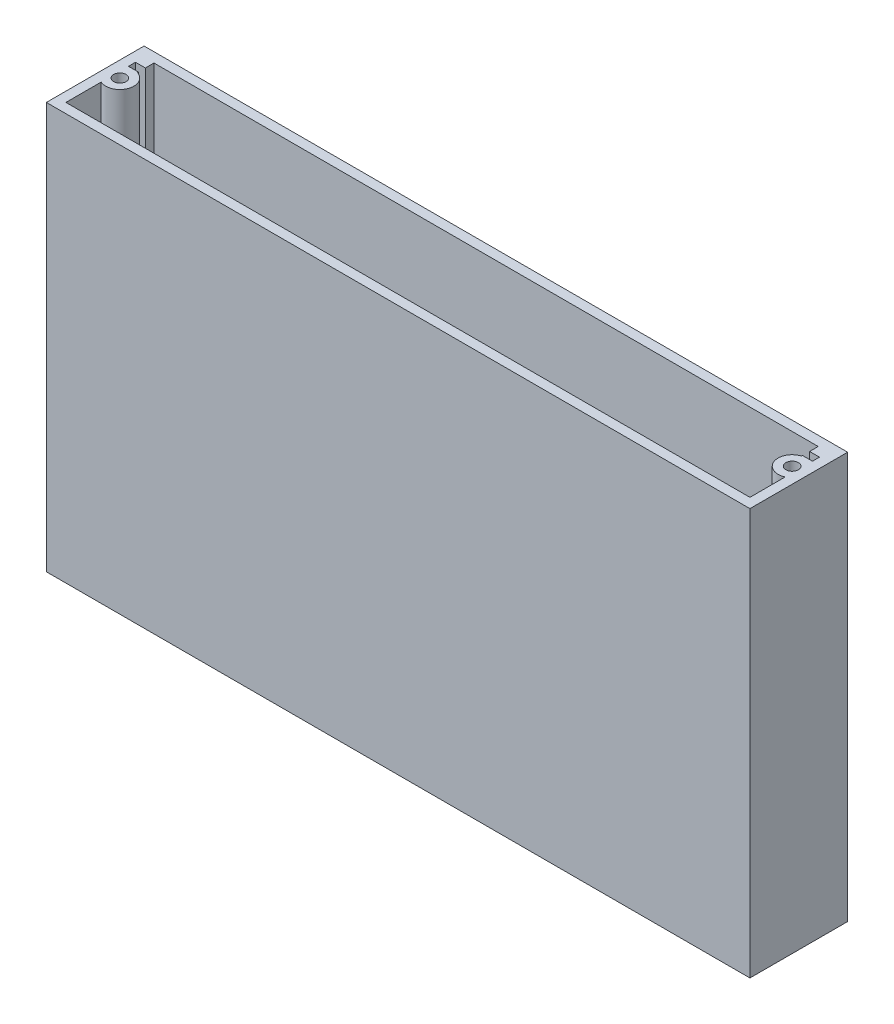
SolidWorks part; units mm, degrees
ref_plane "Front Plane" through (0, 0, 0) normal (0, 0, 1) x (1, 0, 0)
ref_plane "Top Plane" through (0, 0, 0) normal (0, 1, 0) x (1, 0, 0)
ref_plane "Right Plane" through (0, 0, 0) normal (1, 0, 0) x (0, 0, -1)
sketch "Sketch1" plane through (0, 0, 0) normal (0, 1, 0) x (1, 0, 0)
  line L1 (0, 0) -> (228.6, 0)
  line L2 (0, 0) -> (0, 31.75)
  line L3 (0, 31.75) -> (228.6, 31.75)
  line L4 (228.6, 0) -> (228.6, 31.75)
  dimension "D1" = 228.6
  dimension "D2" = 31.75
extrude "Boss-Extrude1" add sketch "Sketch1" along normal blind 132.08
sketch "Sketch2" plane through (0, 132.08, 0) normal (0, 1, 0) x (1, 0, 0)
  line L0 (0, 31.75) -> (0, 0) construction
  line L1 (3.175, 3.175) -> (225.425, 3.175)
  line L2 (3.175, 3.175) -> (3.175, 28.575)
  line L3 (3.175, 28.575) -> (225.425, 28.575)
  line L4 (225.425, 3.175) -> (225.425, 28.575)
  line L5 (228.6, 0) -> (228.6, 31.75) construction
  line L6 (0, 0) -> (228.6, 0) construction
  line L7 (228.6, 31.75) -> (0, 31.75) construction
  dimension "D1" = 3.175
  dimension "D2" = 3.175
  dimension "D3" = 3.175
  dimension "D4" = 3.175
extrude "Cut-Extrude1" cut sketch "Sketch2" against normal blind 128.905
sketch "Sketch3" plane through (0, 3.175, 0) normal (0, 1, 0) x (1, 0, 0)
  line L0 (3.175, 28.575) -> (3.175, 3.175) construction
  line L1 (3.175, 25.781) -> (6.392, 25.781)
  line L2 (3.175, 25.781) -> (3.175, 29.932)
  line L3 (3.175, 29.932) -> (6.392, 29.932)
  line L4 (6.392, 25.781) -> (6.392, 29.932)
  line L5 (3.175, 28.575) -> (3.175, 3.175) construction
  line L6 (3.175, 18.415) -> (6.392, 18.415)
  line L7 (3.175, 18.415) -> (3.175, 23.495)
  line L8 (3.175, 23.495) -> (6.392, 23.495)
  line L9 (6.392, 18.415) -> (6.392, 23.495)
  line L11 (225.425, 28.575) -> (3.175, 28.575) construction
  dimension "D1" = 2.286
  dimension "D2" = 10.16
  dimension "D3" = 5.08
extrude "Boss-Extrude2" add sketch "Sketch3" along normal up to surface (128.905 mm away) up to face at (114.3, 132.08, -15.875)
ref_plane "Plane1" through (114.3, 0, 0) normal (-1, 0, 0) x (0, 0, 1)
mirror "Mirror1" about plane through (114.3, 0, 0) normal (-1, 0, 0) of "Boss-Extrude2"
sketch "Sketch4" plane through (0, 3.175, 0) normal (0, 1, 0) x (1, 0, 0)
  line L0 (228.6, 31.75) -> (0, 31.75) construction
  line L1 (0, 31.75) -> (0, 0) construction
  line L2 (228.6, 0) -> (228.6, 31.75) construction
  circle A0 centre (5.08, 18.796) radius 4.572
  circle A1 centre (223.52, 18.796) radius 4.572
  dimension "D1" = 9.144
  dimension "D2" = 12.954
  dimension "D3" = 5.08
  dimension "D4" = 5.08
extrude "Boss-Extrude3" add sketch "Sketch4" along normal up to surface (128.905 mm away) up to face at (114.3, 132.08, -20.8915)
sketch "Sketch5" plane through (0, 132.08, 0) normal (0, 1, 0) x (1, 0, 0)
  circle A0 centre (5.08, 18.796) radius 2.032
  circle A1 centre (223.52, 18.796) radius 2.032
  dimension "D1" = 4.064
  dimension "D2" = 4.064
extrude "Cut-Extrude2" cut sketch "Sketch5" against normal blind 123.825
